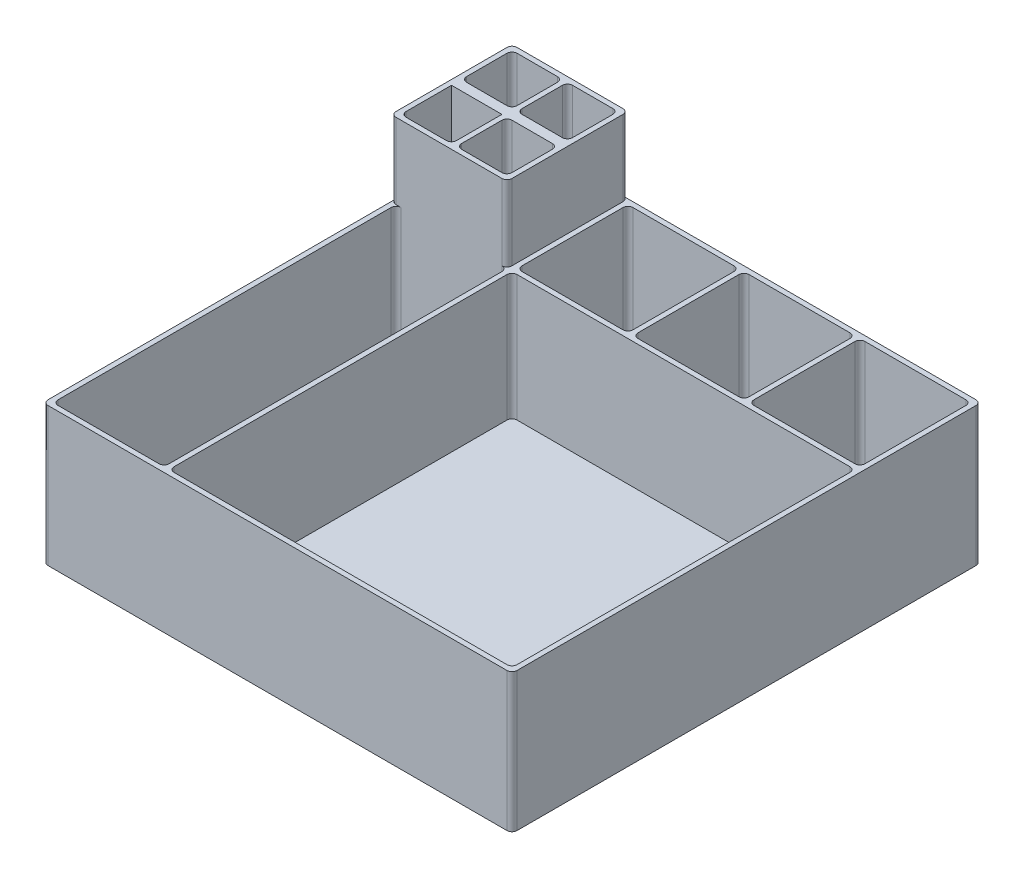
SolidWorks part; units mm, degrees
ref_plane "Front Plane" through (0, 0, 0) normal (0, 0, 1) x (1, 0, 0)
ref_plane "Top Plane" through (0, 0, 0) normal (0, 1, 0) x (1, 0, 0)
ref_plane "Right Plane" through (0, 0, 0) normal (1, 0, 0) x (0, 0, -1)
sketch "Sketch1" plane through (0, 0, 0) normal (0, 1, 0) x (1, 0, 0)
  line L1 (93, -93) -> (-93, -93)
  line L2 (93, -93) -> (93, 93)
  line L3 (93, 93) -> (-93, 93)
  line L4 (-93, -93) -> (-93, 93)
  line L5 (93, -93) -> (-93, 93) construction
  line L6 (93, 93) -> (-93, -93) construction
  point P0 (0, 0)
  dimension "D1" = 186
  dimension "D2" = 186
extrude "Boss-Extrude1" add sketch "Sketch1" along normal blind 5
sketch "Sketch2" plane through (0, 5, 0) normal (0, 1, 0) x (1, 0, 0)
  line L11 (-93, 93) -> (-70, 93)
  line L12 (-93, 93) -> (-93, 69)
  line L13 (-93, 69) -> (-70, 69)
  line L14 (-70, 93) -> (-70, 69)
  line L15 (-91, 91) -> (-71, 91)
  line L16 (-91, 91) -> (-91, 71)
  line L17 (-91, 71) -> (-71, 71)
  line L18 (-71, 91) -> (-71, 71)
  dimension "D1" = 20
  dimension "D2" = 20
  dimension "D3" = 2
  dimension "D4" = 1
  dimension "D5" = 2
  dimension "D6" = 2
extrude "Boss-Extrude2" add sketch "Sketch2" along normal blind 80
pattern_linear "LPattern1" count 2 spacing 22 along (1, 0, 0) of "Boss-Extrude2"
mirror "Mirror1" about plane through (-93, 85, -69) normal (0, 0, -1) of "LPattern1", "Boss-Extrude2"
sketch "Sketch3" plane through (0, 5, 0) normal (0, 1, 0) x (1, 0, 0)
  line L1 (-48, 93) -> (-47, 93)
  line L2 (-48, 93) -> (-48, 45)
  line L3 (-48, 45) -> (-47, 45)
  line L4 (-47, 93) -> (-47, 45)
  dimension "D1" = 1
extrude "Boss-Extrude3" add sketch "Sketch3" along normal up to surface (80 mm away) up to face at (-81, 85, -57)
sketch "Sketch4" plane through (0, 5, 0) normal (0, 1, 0) x (1, 0, 0)
  line L0 (-1, 91) -> (-1, 47)
  line L1 (-47, 93) -> (1, 93)
  line L2 (-47, 93) -> (-47, 45)
  line L3 (-47, 45) -> (1, 45)
  line L4 (1, 93) -> (1, 45)
  line L5 (-45, 47) -> (-1, 47)
  line L6 (-45, 91) -> (-45, 47)
  line L7 (-45, 91) -> (-1, 91)
  dimension "D1" = 48
  dimension "D2" = 48
  dimension "D3" = 2
extrude "Boss-Extrude4" add sketch "Sketch4" along normal blind 50
pattern_linear "LPattern2" count 3 spacing 46 along (1, 0, 0) of "Boss-Extrude4"
pattern_linear "LPattern3" count 4 spacing 46 along (0, 0, 1) of "LPattern2", "Boss-Extrude4"
sketch "Sketch6" plane through (0, 5, 0) normal (0, 1, 0) x (1, 0, 0)
  line L0 (-47, -91) -> (-91, -91)
  line L1 (-47, -93) -> (-93, -93)
  line L2 (-47, -93) -> (-47, -91)
  line L3 (-91, 45) -> (-93, 45)
  line L4 (-93, -93) -> (-93, 45)
  line L5 (-91, -91) -> (-91, 45)
  line L8 (-49, -91) -> (-49, 43) construction
  line L9 (-49, 43) -> (-91, 43) construction
  line L10 (-49, -91) -> (-91, -91) construction
  line L11 (-47, -93) -> (-47, 45) construction
  line L12 (-91, -91) -> (-91, 43) construction
  line L13 (-47, 45) -> (-93, 45) construction
  dimension "D1" = 2
extrude "Boss-Extrude6" add sketch "Sketch6" along normal blind 50
sketch "Sketch9" plane through (0, 5, 0) normal (0, 1, 0) x (1, 0, 0)
  line L1 (-45, 45) -> (91, 45)
  line L2 (-45, 45) -> (-45, -91)
  line L3 (-45, -91) -> (91, -91)
  line L4 (91, 45) -> (91, -91)
extrude "Cut-Extrude2" cut sketch "Sketch9" along normal blind 50
fillet "Fillet1" radius 2 39 edges at (-69, 45, -47) (-49, 45, -47) (-49, 45, -67) (-69, 45, -67) (-47, 70, -93) (-45, 30, -91) (-45, 30, -47) (-1, 30, -47) (-1, 30, -91) (47, 30, -47) (1, 30, -91) (1, 30, -47) (45, 30, -47) (45, 30, -91) (47, 30, -91) (91, 30, -47) (91, 30, -91) (-91, 45, -71) (-71, 45, -71) (-71, 45, -91) (-91, 45, -91) (-47, 30, -45) (-45, 30, -45) (-45, 30, 91) (91, 30, -45) (91, 30, 91) (-47, 30, 91) (-91, 30, 91) (-91, 30, -45) (-69, 45, -71) (-49, 45, -71) (-49, 45, -91) (-69, 45, -91) (-93, 42.5, -93) (93, 27.5, -93) (93, 27.5, 93) (-93, 27.5, 93) (-91, 45, -47) (-71, 45, -47)
fillet "Fillet2" radius 2 2 edges at (-47, 70, -45) (-93, 70, -45)
